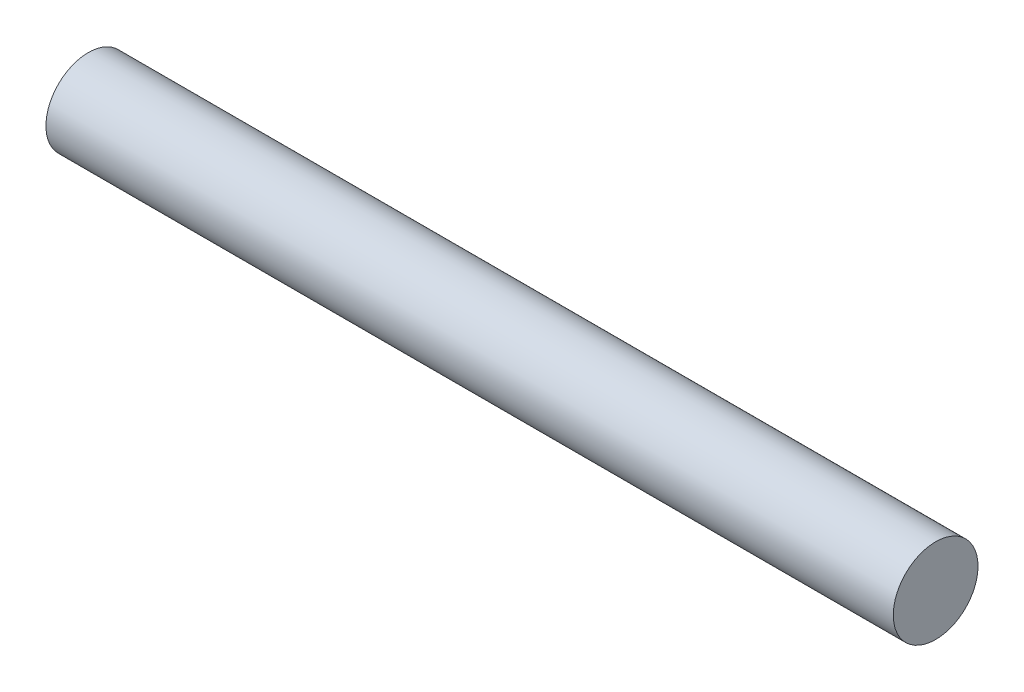
SolidWorks part; units mm, degrees
material "Titanium"
ref_plane "Front Plane" through (0, 0, 0) normal (0, 0, 1) x (1, 0, 0)
ref_plane "Top Plane" through (0, 0, 0) normal (0, 1, 0) x (1, 0, 0)
ref_plane "Right Plane" through (0, 0, 0) normal (1, 0, 0) x (0, 0, -1)
sketch "Sketch1" plane through (0, 0, 0) normal (1, 0, 0) x (0, 0, -1)
  circle A0 centre (0, 0) radius 10
  dimension "D1" = 20
extrude "Extrude1" add sketch "Sketch1" along normal blind 200
